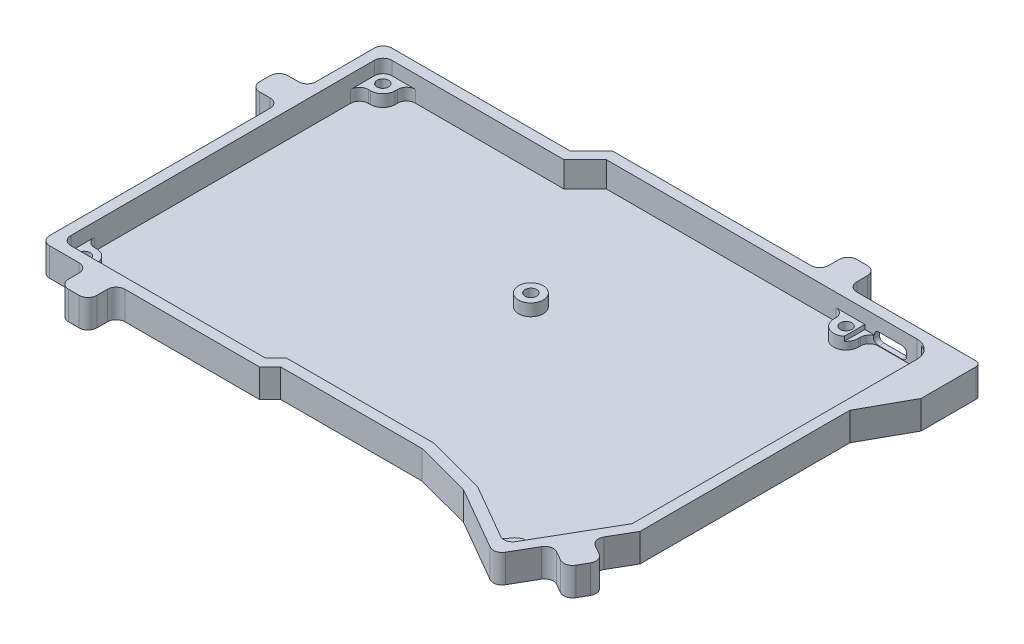
SolidWorks part; units mm, degrees
ref_plane "Front Plane" through (0, 0, 0) normal (0, 0, 1) x (1, 0, 0)
ref_plane "Top Plane" through (0, 0, 0) normal (0, 1, 0) x (1, 0, 0)
ref_plane "Right Plane" through (0, 0, 0) normal (1, 0, 0) x (0, 0, -1)
sketch "Sketch1" plane through (0, 0, 0) normal (0, 1, 0) x (1, 0, 0)
  line L0 (74.625, 48) -> (-17.625, 48) construction
  line L1 (-74.625, -48) -> (74.625, -48) construction
  line L2 (-74.625, -48) -> (-74.625, 48) construction
  line L3 (-74.625, 48) -> (74.625, 48) construction
  line L4 (74.625, -48) -> (74.625, 48) construction
  line L5 (-74.625, -48) -> (74.625, 48) construction
  line L6 (-74.625, 48) -> (74.625, -48) construction
  line L7 (-17.625, 48) -> (-17.625, 42) construction
  line L8 (-17.625, 42) -> (-23.625, 42) construction
  line L9 (-17.625, 48) -> (-23.625, 42) construction
  line L10 (-23.625, 42) -> (-74.625, 42) construction
  line L11 (-74.625, 42) -> (-74.625, -48) construction
  line L12 (-74.625, -48) -> (-17.625, -48) construction
  line L13 (-17.625, -48) -> (-17.625, -45) construction
  line L14 (-17.625, -45) -> (-14.625, -45) construction
  line L15 (-14.625, -45) -> (-17.625, -48) construction
  line L16 (-14.625, -45) -> (27.375, -45) construction
  line L17 (74.625, 48) -> (74.625, -37) construction
  line L18 (27.375, -45) -> (44.3045, -45) construction
  line L19 (44.3045, -45) -> (44.3045, -49.5167) construction
  line L20 (44.3045, -49.5167) -> (27.375, -45) construction
  line L21 (44.3045, -49.5167) -> (61.6269, -49.5167) construction
  line L22 (61.6269, -49.5167) -> (61.6269, -59.5048) construction
  line L23 (44.3045, -49.5167) -> (61.6269, -59.5048) construction
  line L24 (74.625, -37) -> (61.6269, -59.5048) construction
  line L25 (75.125, -37.134) -> (61.81, -60.1875)
  line L26 (44.1119, -49.9828) -> (61.81, -60.1875)
  line L27 (44.1119, -49.9828) -> (27.3094, -45.5)
  line L28 (-14.4179, -45.5) -> (27.3094, -45.5)
  line L29 (-14.4179, -45.5) -> (-17.4179, -48.5)
  line L30 (-75.125, -48.5) -> (-17.4179, -48.5)
  line L31 (-75.125, 42.5) -> (-75.125, -48.5)
  line L32 (-23.8321, 42.5) -> (-75.125, 42.5)
  line L33 (-17.8321, 48.5) -> (-23.8321, 42.5)
  line L34 (75.125, 48.5) -> (-17.8321, 48.5)
  line L35 (75.125, 48.5) -> (75.125, -37.134)
  line L36 (78.125, -37.9381) -> (62.9085, -64.2839)
  line L37 (42.9562, -52.7794) -> (62.9085, -64.2839)
  line L38 (42.9562, -52.7794) -> (26.9161, -48.5)
  line L39 (-13.1753, -48.5) -> (26.9161, -48.5)
  line L40 (-13.1753, -48.5) -> (-16.1753, -51.5)
  line L41 (-78.125, -51.5) -> (-16.1753, -51.5)
  line L42 (-78.125, 45.5) -> (-78.125, -51.5)
  line L43 (-25.0747, 45.5) -> (-78.125, 45.5)
  line L44 (-19.0747, 51.5) -> (-25.0747, 45.5)
  line L45 (78.125, 51.5) -> (-19.0747, 51.5)
  line L46 (78.125, 51.5) -> (78.125, -37.9381)
  point P0 (0, 0)
  dimension "D1" = 149.25
  dimension "D2" = 96
  dimension "D3" = 92.25
  dimension "D4" = 6
  dimension "D5" = 6
  dimension "D6" = 57
  dimension "D7" = 3
  dimension "D8" = 3
  dimension "D9" = 42
  dimension "D10" = 85
  dimension "D11" = 16.9295
  dimension "D12" = 4.5167
  dimension "D13" = 17.3224
  dimension "D14" = 9.9881
  dimension "D15" = 0.5
  dimension "D16" = 3
extrude "Boss-Extrude1" add sketch "Sketch1" along normal blind 7.2
sketch "Sketch2" plane through (0, 0, 0) normal (0, -1, 0) x (1, 0, 0)
  line L11 (78.125, -51.5) -> (78.125, 37.9381)
  line L12 (78.125, 37.9381) -> (62.9085, 64.2839)
  line L13 (62.9085, 64.2839) -> (42.9562, 52.7794)
  line L14 (42.9562, 52.7794) -> (26.9161, 48.5)
  line L15 (26.9161, 48.5) -> (-13.1753, 48.5)
  line L16 (-13.1753, 48.5) -> (-16.1753, 51.5)
  line L17 (-16.1753, 51.5) -> (-78.125, 51.5)
  line L18 (-78.125, 51.5) -> (-78.125, -45.5)
  line L19 (-78.125, -45.5) -> (-25.0747, -45.5)
  line L20 (-25.0747, -45.5) -> (-19.0747, -51.5)
  line L21 (-19.0747, -51.5) -> (78.125, -51.5)
  line L22 (78.125, -51.5) -> (78.125, 37.9381)
  line L23 (78.125, 37.9381) -> (62.9085, 64.2839)
  line L24 (62.9085, 64.2839) -> (42.9562, 52.7794)
  line L25 (42.9562, 52.7794) -> (26.9161, 48.5)
  line L26 (26.9161, 48.5) -> (-13.1753, 48.5)
  line L27 (-13.1753, 48.5) -> (-16.1753, 51.5)
  line L28 (-16.1753, 51.5) -> (-78.125, 51.5)
  line L29 (-78.125, 51.5) -> (-78.125, -45.5)
  line L30 (-78.125, -45.5) -> (-25.0747, -45.5)
  line L31 (-25.0747, -45.5) -> (-19.0747, -51.5)
  line L32 (-19.0747, -51.5) -> (78.125, -51.5)
  dimension "D1" = 0
extrude "Boss-Extrude2" add sketch "Sketch2" along normal blind 0.8
fillet "Fillet1" radius 2.5 3 edges at (-75.125, 3.6, 48.5) (61.81, 3.6, 60.1875) (-75.125, 3.6, -42.5)
fillet "Fillet2" radius 2.5 3 edges at (-78.125, 3.2, 51.5) (62.9085, 3.2, 64.2839) (-78.125, 3.2, -45.5)
sketch "Sketch3" plane through (0, 0, 0) normal (0, 1, 0) x (1, 0, 0)
  line L0 (-68.5, 39.3) -> (-68.5, 42.5)
  line L1 (-72, 35.8) -> (-75.125, 35.8)
  line L2 (-72, -41.8) -> (-75.125, -41.8)
  line L3 (-68.5, -45.3) -> (-68.5, -48.5)
  line L4 (-75.125, -41.8) -> (-75.125, -46)
  line L5 (-72.625, -48.5) -> (-68.5, -48.5)
  line L6 (-70.5823, 42.5) -> (-68.5, 42.5)
  line L7 (-75.125, 35.8) -> (-75.125, 37.7238)
  line L8 (60.6718, -55.8182) -> (-24915.0304, -43371.1077) construction
  line L9 (61.0382, -56.1838) -> (43376.3277, -25031.886) construction
  line L10 (62.3533, -52.9019) -> (65.1013, -54.4891)
  line L11 (-75.125, 40) -> (-75.125, -46)
  line L12 (-72.625, -48.5) -> (-17.4179, -48.5)
  line L13 (-17.4179, -48.5) -> (-14.4179, -45.5)
  line L14 (-14.4179, -45.5) -> (27.3094, -45.5)
  line L15 (27.3094, -45.5) -> (44.1119, -49.9828)
  line L16 (44.1119, -49.9828) -> (59.6458, -58.9397)
  line L17 (63.0594, -58.0242) -> (75.125, -37.134)
  line L18 (75.125, -37.134) -> (75.125, 48.5)
  line L19 (75.125, 48.5) -> (-17.8321, 48.5)
  line L20 (-17.8321, 48.5) -> (-23.8321, 42.5)
  line L21 (-23.8321, 42.5) -> (-72.625, 42.5)
  line L22 (-75.125, 40) -> (-75.125, -46) construction
  line L23 (-72.625, -48.5) -> (-17.4179, -48.5) construction
  line L24 (-17.4179, -48.5) -> (-14.4179, -45.5) construction
  line L25 (-14.4179, -45.5) -> (27.3094, -45.5) construction
  line L26 (27.3094, -45.5) -> (44.1119, -49.9828) construction
  line L27 (44.1119, -49.9828) -> (59.6458, -58.9397) construction
  line L28 (63.0594, -58.0242) -> (75.125, -37.134) construction
  line L29 (75.125, -37.134) -> (75.125, 48.5) construction
  line L30 (75.125, 48.5) -> (-17.8321, 48.5) construction
  line L31 (-17.8321, 48.5) -> (-23.8321, 42.5) construction
  line L32 (-23.8321, 42.5) -> (-72.625, 42.5) construction
  line L33 (57.5729, -54.1857) -> (56.033, -56.8565)
  line L34 (56.033, -56.8565) -> (59.6458, -58.9397)
  line L35 (63.0594, -58.0242) -> (65.1013, -54.4891)
  line L36 (56.645, 45.4) -> (56.645, 48.5)
  line L37 (49.645, 48.5) -> (51.5202, 48.5)
  line L38 (49.645, 48.5) -> (49.645, 45.4)
  line L39 (57.6296, -57.7771) -> (56.033, -56.8565)
  circle A0 centre (-72, 39.3) radius 3.5
  circle A1 centre (-72, -45.3) radius 3.5
  circle A2 centre (60.605, -55.934) radius 3.5
  circle A3 centre (53.145, 45.4) radius 3.5
  arc A4 (-75.125, -46) -> (-72.625, -48.5) centre (-72.625, -46) ccw
  arc A5 (59.6458, -58.9397) -> (63.0594, -58.0242) centre (60.8946, -56.7739) ccw
  arc A7 (-72.625, 42.5) -> (-75.125, 40) centre (-72.625, 40) ccw
  arc A8 (-75.125, -46) -> (-72.625, -48.5) centre (-72.625, -46) ccw
  arc A9 (59.6458, -58.9397) -> (63.0594, -58.0242) centre (60.8946, -56.7739) ccw
  arc A11 (-72.625, 42.5) -> (-75.125, 40) centre (-72.625, 40) ccw
  circle A12 centre (0.325, 8.92) radius 3.5
  point P35 (62.3533, -52.9019)
  point P39 (58.8567, -58.9661)
  point P43 (57.5729, -54.1857)
  point P53 (57.6296, -57.7771)
  line M22 (-75.125, 40) -> (-75.125, -46)
  arc M23 (-75.125, -46) -> (-72.625, -48.5) centre (-72.625, -46) ccw
  line M24 (-72.625, -48.5) -> (-17.4179, -48.5)
  line M28 (44.1119, -49.9828) -> (59.6458, -58.9397)
  arc M29 (59.6458, -58.9397) -> (63.0594, -58.0242) centre (60.8946, -56.7739) ccw
  line M30 (63.0594, -58.0242) -> (75.125, -37.134)
  line M33 (75.125, 48.5) -> (-17.8321, 48.5)
  line M35 (-23.8321, 42.5) -> (-72.625, 42.5)
  arc M36 (-72.625, 42.5) -> (-75.125, 40) centre (-72.625, 40) ccw
  dimension "D2" = 7
  dimension "D3" = 7
  dimension "D4" = 7
  dimension "D5" = 7
  dimension "D15" = 7
  dimension "D6" = 3.125
  dimension "D7" = 3.2
  dimension "D8" = 3.2
  dimension "D9" = 3.125
  dimension "D10" = 14.52
  dimension "D11" = 18.8
  dimension "D12" = 3.1
  dimension "D13" = 21.98
  dimension "D16" = 75.45
  dimension "D17" = 33.58
  dimension "D1" = 0
extrude "Boss-Extrude3" add sketch "Sketch3" along normal blind 3.4 contours A1 L4 M24 M23 | A1 L2 M22 | A0 L0 M35 | A0 M35 M36 M22 | A0 L1 M22 | A12 | A3 M33 | A3 L36 M33 | A3 L38 M33 | A2 L35 L10 | A2 L34 M30 M29 | A2 L33 M28 | A1 L5 L3
sketch "Sketch5" plane through (0, 3.4, 0) normal (0, 1, 0) x (1, 0, 0)
  arc A0 (49.645, 45.4) -> (56.645, 45.4) centre (53.145, 45.4) ccw construction
  arc A1 (62.3533, -52.9019) -> (57.5729, -54.1857) centre (60.605, -55.934) ccw construction
  arc A2 (-68.5, -45.3) -> (-72, -41.8) centre (-72, -45.3) ccw construction
  circle A3 centre (0.325, 8.92) radius 3.5 construction
  arc A4 (-72, 35.8) -> (-68.5, 39.3) centre (-72, 39.3) ccw construction
  arc A5 (49.645, 45.4) -> (56.645, 45.4) centre (53.145, 45.4) ccw construction
  arc A6 (62.3533, -52.9019) -> (57.5729, -54.1857) centre (60.605, -55.934) ccw construction
  arc A7 (-68.5, -45.3) -> (-72, -41.8) centre (-72, -45.3) ccw construction
  circle A8 centre (0.325, 8.92) radius 3.5 construction
  arc A9 (-72, 35.8) -> (-68.5, 39.3) centre (-72, 39.3) ccw construction
  circle A10 centre (-72, 39.3) radius 1.65
  circle A11 centre (0.325, 8.92) radius 1.65
  circle A12 centre (53.145, 45.4) radius 1.65
  circle A13 centre (60.605, -55.934) radius 1.65
  circle A14 centre (-72, -45.3) radius 1.65
  dimension "D1" = 3.3
  dimension "D2" = 3.3
  dimension "D3" = 3.3
  dimension "D4" = 3.3
  dimension "D5" = 3.3
extrude "Cut-Extrude1" cut sketch "Sketch5" against normal blind 2.5
fillet "Fillet3" radius 2.5 8 edges at (65.1013, 1.7, 54.4891) (49.645, 1.7, -48.5) (56.645, 1.7, -48.5) (-75.125, 1.7, -35.8) (-68.5, 1.7, -42.5) (-75.125, 1.7, 41.8) (56.033, 1.7, 56.8565) (-68.5, 1.7, 48.5)
sketch "Sketch8" plane through (0, 0, -51.5) normal (0, 0, -1) x (-1, 0, 0)
  line L1 (-67.23, 0.14) -> (-58.09, 0.14)
  line L2 (-67.23, 0.14) -> (-67.23, 3.5)
  line L3 (-67.23, 3.5) -> (-58.09, 3.5)
  line L4 (-58.09, 0.14) -> (-58.09, 3.5)
  line L5 (-67.23, 0.14) -> (-58.09, 3.5) construction
  line L6 (-67.23, 3.5) -> (-58.09, 0.14) construction
  line L7 (19.0747, -0.8) -> (-78.125, -0.8) construction
  line L9 (-78.125, 7.2) -> (-78.125, -0.8) construction
  point P0 (-62.66, 1.82)
  dimension "D1" = 3.36
  dimension "D2" = 9.14
  dimension "D3" = 10.895
  dimension "D4" = 0.94
extrude "Cut-Extrude4" cut sketch "Sketch8" against normal up to next
fillet "Fillet5" radius 1.3 4 edges at (67.23, 0.14, -50) (58.09, 0.14, -49.8832) (58.09, 3.5, -50) (67.23, 3.5, -50)
sketch "Sketch9" plane through (0, 0, -51.5) normal (0, 0, -1) x (-1, 0, 0)
  line L0 (-67.23, 2.2) -> (-67.23, 1.44) construction
  line L1 (-65.93, 0.14) -> (-59.39, 0.14) construction
  line L2 (-58.09, 1.44) -> (-58.09, 2.2) construction
  line L3 (-59.39, 3.5) -> (-65.93, 3.5) construction
  line L4 (-67.23, 2.2) -> (-67.23, 1.44) construction
  line L5 (-65.93, 0.14) -> (-59.39, 0.14) construction
  line L6 (-58.09, 1.44) -> (-58.09, 2.2) construction
  line L7 (-59.39, 3.5) -> (-65.93, 3.5) construction
  line L8 (-69.73, 2.2) -> (-69.73, 1.44)
  line L9 (-65.93, -2.36) -> (-59.39, -2.36)
  line L10 (-55.59, 1.44) -> (-55.59, 2.2)
  line L11 (-59.39, 6) -> (-65.93, 6)
  line L12 (-69.73, 1.44) -> (-69.73, -0.8)
  line L13 (19.0747, -0.8) -> (-78.125, -0.8) construction
  line L14 (-69.73, -0.8) -> (-55.59, -0.8)
  line L15 (-55.59, -0.8) -> (-55.59, 1.44)
  arc A0 (-65.93, 3.5) -> (-67.23, 2.2) centre (-65.93, 2.2) ccw construction
  arc A1 (-67.23, 1.44) -> (-65.93, 0.14) centre (-65.93, 1.44) ccw construction
  arc A2 (-59.39, 0.14) -> (-58.09, 1.44) centre (-59.39, 1.44) ccw construction
  arc A3 (-58.09, 2.2) -> (-59.39, 3.5) centre (-59.39, 2.2) ccw construction
  arc A4 (-65.93, 3.5) -> (-67.23, 2.2) centre (-65.93, 2.2) ccw construction
  arc A5 (-67.23, 1.44) -> (-65.93, 0.14) centre (-65.93, 1.44) ccw construction
  arc A6 (-59.39, 0.14) -> (-58.09, 1.44) centre (-59.39, 1.44) ccw construction
  arc A7 (-58.09, 2.2) -> (-59.39, 3.5) centre (-59.39, 2.2) ccw construction
  arc A8 (-69.73, 1.44) -> (-65.93, -2.36) centre (-65.93, 1.44) ccw
  arc A9 (-59.39, -2.36) -> (-55.59, 1.44) centre (-59.39, 1.44) ccw
  arc A10 (-55.59, 2.2) -> (-59.39, 6) centre (-59.39, 2.2) ccw
  arc A11 (-65.93, 6) -> (-69.73, 2.2) centre (-65.93, 2.2) ccw
  line M27 (-78.125, -0.8) -> (19.0747, -0.8)
  dimension "D1" = 2.5
extrude "Cut-Extrude5" cut sketch "Sketch9" against normal blind 1.6 contours A8 L12 M27 | A9 L15 M27
sketch "Sketch10" plane through (78.125, 0, 0) normal (1, 0, 0) x (0, 0, -1)
  line L0 (51.5, 7.2) -> (51.5, -0.8) construction
  line L1 (48.5, 7.2) -> (36.5, 7.2)
  line L2 (48.5, 7.2) -> (48.5, 0)
  line L3 (48.5, 0) -> (36.5, 0)
  line L4 (36.5, 7.2) -> (36.5, 0)
  line L5 (-37.9381, 7.2) -> (51.5, 7.2) construction
  line L6 (-37.134, 0) -> (48.5, 0) construction
  line L8 (-37.134, 0) -> (48.5, 0) construction
  dimension "D1" = 3
  dimension "D3" = 12
extrude "Cut-Extrude6" cut sketch "Sketch10" against normal up to next
sketch "Sketch12" plane through (78.125, 0, 0) normal (1, 0, 0) x (0, 0, -1)
  line L0 (36.5, 7.2) -> (34.5, 7.2)
  line L1 (-37.9381, 7.2) -> (36.5, 7.2) construction
  line L2 (34.5, 7.2) -> (34.5, -0.8)
  line L3 (51.5, -0.8) -> (-37.9381, -0.8) construction
  line L4 (34.5, -0.8) -> (51.5, -0.8)
  line L5 (51.5, -0.8) -> (51.5, 7.2)
  line L6 (51.5, 7.2) -> (49.5, 7.2)
  line L7 (48.5, 7.2) -> (51.5, 7.2) construction
  line L8 (49.5, 7.2) -> (49.5, 0)
  line L9 (49.5, 0) -> (36.5, 0)
  line L10 (36.5, 0) -> (36.5, 7.2)
  dimension "D1" = 2
  dimension "D2" = 2
extrude "Boss-Extrude4" add sketch "Sketch12" along normal blind 5.2
sketch "Sketch13" plane through (83.325, 0, 0) normal (1, 0, 0) x (0, 0, -1)
  line L1 (34.5, -0.8) -> (51.5, -0.8)
  line L2 (34.5, -0.8) -> (34.5, 7.2)
  line L3 (34.5, 7.2) -> (51.5, 7.2)
  line L4 (51.5, -0.8) -> (51.5, 7.2)
extrude "Boss-Extrude5" add sketch "Sketch13" along normal blind 2
sketch "Sketch14" plane through (0, 0, -49.5) normal (0, 0, 1) x (1, 0, 0)
  line L0 (83.325, 0) -> (78.125, 0) construction
  line L2 (83.325, 7.2) -> (78.125, 7.2) construction
  line L3 (83.325, 7.2) -> (78.125, 7.2) construction
  circle A0 centre (80.725, 3.1) radius 2.6
  point P4 (80.725, 7.2)
  dimension "D2" = 5.2
  dimension "D1" = 3.1
extrude "Cut-Extrude7" cut sketch "Sketch14" against normal up to next
sketch "Sketch15" plane through (0, 7.2, 0) normal (0, 1, 0) x (1, 0, 0)
  line L0 (78.125, 49.5) -> (78.125, 48.5)
  line L1 (78.125, 48.5) -> (73.125, 48.5)
  line L2 (78.125, 48.5) -> (59.145, 48.5) construction
  line L3 (73.125, 48.5) -> (78.125, 49.5)
  dimension "D1" = 5
extrude "Cut-Extrude8" cut sketch "Sketch15" against normal up to surface (7.2 mm away)
sketch "Sketch16" plane through (0, 7.2, 0) normal (0, 1, 0) x (1, 0, 0)
  line L0 (85.325, 34.5) -> (78.125, 34.5)
  line L1 (78.125, 34.5) -> (78.125, 21.5)
  line L2 (78.125, -37.9381) -> (78.125, 34.5) construction
  line L3 (78.125, 21.5) -> (85.325, 34.5)
  dimension "D1" = 13
extrude "Boss-Extrude6" add sketch "Sketch16" against normal up to surface (8 mm away) up to face at (19.5234, -0.8, -2.161)
sketch "Sketch17" plane through (0, 7.2, 0) normal (0, 1, 0) x (1, 0, 0)
  line L0 (85.325, 51.5) -> (85.325, 34.5)
  line L1 (85.325, 34.5) -> (81.725, 28)
  line L2 (78.125, 21.5) -> (85.325, 34.5) construction
  line L3 (81.725, 28) -> (75.125, 28)
  line L4 (75.125, -37.134) -> (75.125, 36.5) construction
  line L5 (75.125, 28) -> (75.125, 36.5)
  line L6 (75.125, 36.5) -> (75.125, 48.9)
  line L7 (78.125, 49.5) -> (73.125, 48.5) construction
  line L8 (75.125, 48.9) -> (75.125, 51.5)
  line L9 (85.325, 51.5) -> (-19.0747, 51.5) construction
  line L10 (75.125, 51.5) -> (85.325, 51.5)
  line L11 (73.125, 48.5) -> (75.125, 48.5)
  line L12 (73.125, 48.5) -> (73.125, 51.5)
  line L13 (73.125, 51.5) -> (75.125, 51.5)
extrude "Boss-Extrude8" add sketch "Sketch17" against normal blind 0.8
fillet "Fillet6" radius 1 1 edges at (83.325, 3.2, -36.5)
chamfer "Chamfer1" distance 10 angle 29 1 edges at (75.125, 3.2, -36.5)
fillet "Fillet7" radius 5 1 edges at (75.125, 6.8, -48.5)
fillet "Fillet8" radius 1.5 1 edges at (85.325, 3.2, -51.5)
sketch "Sketch18" plane through (75.0134, 0, 43.3255) normal (0.8659, 0, 0.5001) x (0.5001, 0, -0.8659)
  line L0 (-7.7418, 7.2) -> (-7.7418, -0.8) construction
  line L1 (-21.7048, 7.2) -> (6.2213, 7.2) construction
  line L2 (6.2213, -0.8) -> (-21.7048, -0.8) construction
  line L4 (-11.7418, -0.8) -> (-3.7418, -0.8)
  line L5 (-11.7418, -0.8) -> (-11.7418, 7.2)
  line L6 (-11.7418, 7.2) -> (-3.7418, 7.2)
  line L7 (-3.7418, -0.8) -> (-3.7418, 7.2)
  line L8 (-11.7418, -0.8) -> (-3.7418, 7.2) construction
  line L9 (-11.7418, 7.2) -> (-3.7418, -0.8) construction
  point P6 (-7.7418, 3.2)
  dimension "D1" = 8
extrude "Boss-Extrude9" add sketch "Sketch18" along normal blind 8
sketch "Sketch19" plane through (0, 0, -51.5) normal (0, 0, -1) x (-1, 0, 0)
  line L0 (-55.59, -0.8) -> (-55.59, 2.2) construction
  line L2 (19.0747, -0.8) -> (-55.59, -0.8) construction
  line L3 (-83.825, 7.2) -> (19.0747, 7.2) construction
  line L5 (-43.59, 7.2) -> (-43.59, -0.8) construction
  line L7 (-47.59, -0.8) -> (-39.59, -0.8)
  line L8 (-47.59, -0.8) -> (-47.59, 7.2)
  line L9 (-47.59, 7.2) -> (-39.59, 7.2)
  line L10 (-39.59, -0.8) -> (-39.59, 7.2)
  line L11 (-47.59, -0.8) -> (-39.59, 7.2) construction
  line L12 (-47.59, 7.2) -> (-39.59, -0.8) construction
  point P11 (-43.59, 3.2)
  dimension "D1" = 8
  dimension "D2" = 12
extrude "Boss-Extrude10" add sketch "Sketch19" along normal blind 8
sketch "Sketch20" plane through (0, 0, 51.5) normal (0, 0, 1) x (1, 0, 0)
  line L0 (-75.625, 7.2) -> (-16.1753, 7.2) construction
  line L1 (-75.625, 7.2) -> (-16.1753, 7.2) construction
  line L2 (-45.9001, 7.2) -> (-75.625, 7.2) construction
  line L3 (-60.7626, 7.2) -> (-60.7626, -0.8) construction
  line L4 (-16.1753, -0.8) -> (-75.625, -0.8) construction
  line L6 (-64.7626, -0.8) -> (-56.7626, -0.8)
  line L7 (-64.7626, -0.8) -> (-64.7626, 7.2)
  line L8 (-64.7626, 7.2) -> (-56.7626, 7.2)
  line L9 (-56.7626, -0.8) -> (-56.7626, 7.2)
  line L10 (-64.7626, -0.8) -> (-56.7626, 7.2) construction
  line L11 (-64.7626, 7.2) -> (-56.7626, -0.8) construction
  point P8 (-60.7626, 3.2)
  dimension "D1" = 8
extrude "Boss-Extrude11" add sketch "Sketch20" along normal blind 8
sketch "Sketch21" plane through (-78.125, 0, 0) normal (-1, 0, 0) x (0, 0, 1)
  line L0 (-43, 7.2) -> (49, 7.2) construction
  line L1 (-43, 7.2) -> (49, 7.2) construction
  line L2 (3, 7.2) -> (-43, 7.2) construction
  line L3 (-20, 7.2) -> (-20, -0.8) construction
  line L4 (49, -0.8) -> (-43, -0.8) construction
  line L6 (-24, -0.8) -> (-16, -0.8)
  line L7 (-24, -0.8) -> (-24, 7.2)
  line L8 (-24, 7.2) -> (-16, 7.2)
  line L9 (-16, -0.8) -> (-16, 7.2)
  line L10 (-24, -0.8) -> (-16, 7.2) construction
  line L11 (-24, 7.2) -> (-16, -0.8) construction
  point P7 (-20, 3.2)
  dimension "D1" = 8
extrude "Boss-Extrude12" add sketch "Sketch21" along normal blind 8
fillet "Fillet11" radius 2.5 16 edges at (73.142, 3.2, 46.5656) (69.1409, 3.2, 53.4931) (80.0696, 3.2, 50.5667) (76.0684, 3.2, 57.4943) (39.59, 3.2, -51.5) (47.59, 3.2, -51.5) (39.59, 3.2, -59.5) (47.59, 3.2, -59.5) (-56.7626, 3.2, 51.5) (-64.7626, 3.2, 51.5) (-56.7626, 3.2, 59.5) (-64.7626, 3.2, 59.5) (-78.125, 3.2, -16) (-78.125, 3.2, -24) (-86.125, 3.2, -16) (-86.125, 3.2, -24)
sketch "Sketch22" plane through (0, -0.8, 0) normal (0, -1, 0) x (1, 0, 0)
  line L0 (39.59, -55.5) -> (47.59, -55.5) construction
  line L3 (39.59, -57) -> (39.59, -54) construction
  line L4 (47.59, -57) -> (47.59, -54) construction
  line L5 (-83.625, -16) -> (-80.625, -16) construction
  line L6 (-82.125, -16) -> (-82.125, -24) construction
  line L7 (-83.625, -24) -> (-80.625, -24) construction
  line L8 (-64.7626, 55.5) -> (-56.7626, 55.5) construction
  line L9 (-64.7626, 57) -> (-64.7626, 54) construction
  line L10 (-56.7626, 57) -> (-56.7626, 54) construction
  line L11 (72.6047, 55.4937) -> (76.6058, 48.5662) construction
  line L12 (73.9036, 56.2439) -> (71.3058, 54.7435) construction
  line L13 (77.9047, 49.3164) -> (75.3069, 47.816) construction
  circle A0 centre (43.59, -55.5) radius 2.2
  circle A1 centre (-82.125, -20) radius 2.2
  circle A2 centre (-60.7626, 55.5) radius 2.2
  circle A3 centre (74.6052, 52.0299) radius 2.2
  dimension "D1" = 4.4
  dimension "D2" = 4.4
  dimension "D3" = 4.4
  dimension "D4" = 4.4
extrude "Cut-Extrude9" cut sketch "Sketch22" against normal blind 6
sketch "Sketch23" plane through (0, 3.4, 0) normal (0, 1, 0) x (1, 0, 0)
  line L0 (58.89, 48.5) -> (47.145, 48.5) construction
  line L1 (55.385, 41.9) -> (58.89, 41.9)
  line L2 (55.385, 41.9) -> (55.385, 48.5)
  line L3 (55.385, 48.5) -> (58.89, 48.5)
  line L4 (58.89, 41.9) -> (58.89, 48.5)
  line L5 (55.385, 41.9) -> (58.89, 48.5) construction
  line L6 (55.385, 48.5) -> (58.89, 41.9) construction
  circle A1 centre (53.145, 45.4) radius 1.65 construction
  circle A2 centre (53.145, 45.4) radius 1.65 construction
  arc A4 (49.645, 45.4) -> (56.645, 45.4) centre (53.145, 45.4) ccw construction
  arc A5 (49.645, 45.4) -> (56.645, 45.4) centre (53.145, 45.4) ccw construction
  point P0 (57.1375, 45.2)
  point P14 (53.145, 41.9)
  dimension "D1" = 2.24
extrude "Cut-Extrude10" cut sketch "Sketch23" against normal blind 1.25
